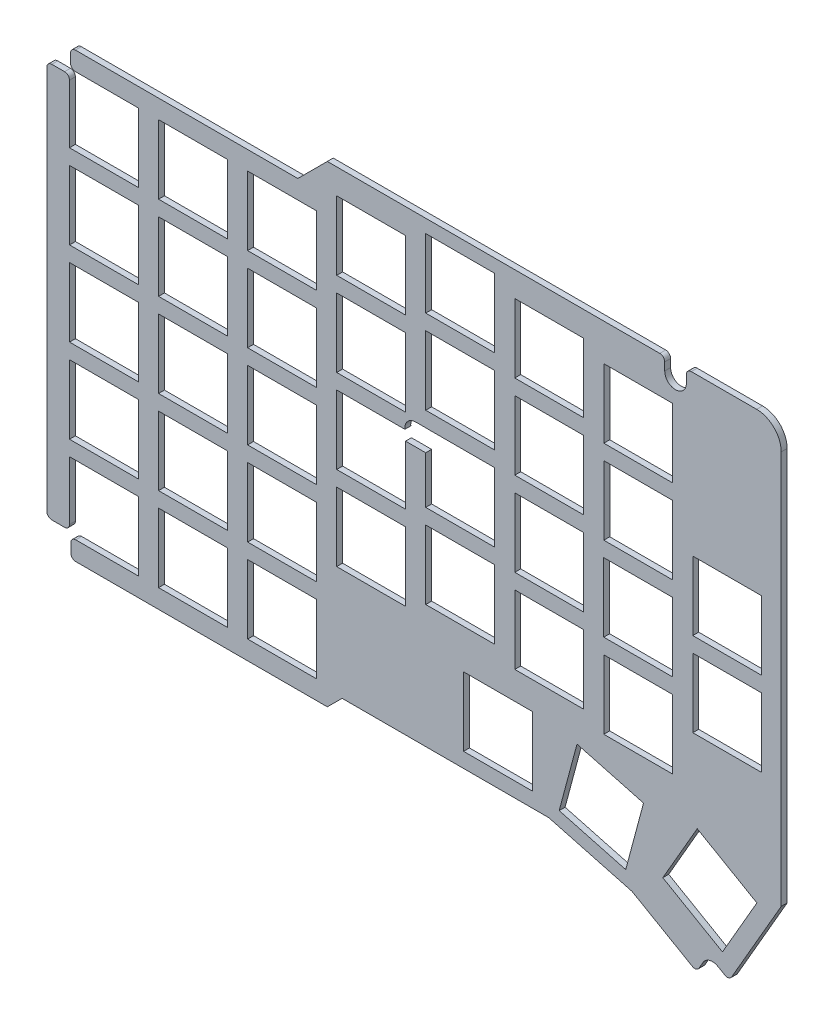
SolidWorks part; units mm, degrees
ref_plane "Front Plane" through (0, 0, 0) normal (0, 0, 1) x (1, 0, 0)
ref_plane "Top Plane" through (0, 0, 0) normal (0, 1, 0) x (1, 0, 0)
ref_plane "Right Plane" through (0, 0, 0) normal (1, 0, 0) x (0, 0, -1)
sketch "Sketch1" plane through (0, 0, 0) normal (0, 0, 1) x (1, 0, 0)
  line L4 (79.33, -202.9) -> (81.33, -202.9)
  line L5 (79.33, -202.9) -> (76.73, -202.9)
  line L6 (81.53, -200.7) -> (81.53, -201.794)
  line L7 (81.53, -200.7) -> (81.53, -198)
  line L8 (81.6, -285.3) -> (81.6, -284.169)
  line L9 (81.6, -284.169) -> (81.6, -288)
  line L11 (82.73, -198) -> (99.78, -198)
  line L12 (82.73, -198) -> (81.53, -198)
  line L13 (76.73, -212.03) -> (76.73, -202.9)
  line L14 (76.73, -283.1) -> (76.73, -212.03)
  line L15 (104.85, -288) -> (81.6, -288)
  line L16 (133.73, -288) -> (113.94, -288)
  line L17 (136.73, -285) -> (133.73, -288)
  line L18 (152.86, -285) -> (136.73, -285)
  line L19 (178.73, -285) -> (161.94, -285)
  line L20 (195.6595, -289.5167) -> (178.73, -285)
  line L22 (79.4, -283.1) -> (81.33, -283.1)
  line L23 (79.4, -283.1) -> (76.73, -283.1)
  line L24 (202.3, -194.6) -> (202.3, -192)
  line L25 (206.7, -194.6) -> (206.7, -192)
  line L26 (206.7, -192) -> (220.98, -192)
  line L29 (-655.8483, 205.3427) -> (210.0949, -294.7997) construction
  line L31 (225.98, -277) -> (215.3978, -295.3219)
  line L32 (225.98, -256.415) -> (225.98, -277)
  line L33 (225.98, -214.605) -> (225.98, -247.025)
  line L34 (225.98, -197) -> (225.98, -205.215)
  line L35 (179.02, -192) -> (202.3, -192)
  line L36 (136.73, -192) -> (169.96, -192)
  line L37 (133.73, -192) -> (136.73, -192)
  line L38 (127.73, -198) -> (133.73, -192)
  line L39 (108.89, -198) -> (127.73, -198)
  line L40 (152.86, -285) -> (161.94, -285)
  line L41 (225.98, -256.415) -> (225.98, -247.025)
  line L42 (225.98, -205.215) -> (225.98, -214.605)
  line L43 (179.02, -192) -> (169.96, -192)
  line L44 (108.89, -198) -> (99.78, -198)
  line L45 (104.85, -288) -> (113.94, -288)
  line L56 (81.6, -284.169) -> (95.33, -284.169)
  line L57 (81.33, -283.1) -> (81.33, -270.169)
  line L58 (81.33, -270.169) -> (95.33, -270.169)
  line L59 (95.33, -284.169) -> (95.33, -270.169)
  line L62 (99.43, -284.169) -> (113.43, -284.169)
  line L63 (99.43, -284.169) -> (99.43, -270.169)
  line L64 (99.43, -270.169) -> (113.43, -270.169)
  line L65 (113.43, -284.169) -> (113.43, -270.169)
  line L66 (99.43, -284.169) -> (113.43, -270.169) construction
  line L67 (99.43, -270.169) -> (113.43, -284.169) construction
  line L68 (81.33, -267.094) -> (95.33, -267.094)
  line L69 (81.33, -267.094) -> (81.33, -253.094)
  line L70 (81.33, -253.094) -> (95.33, -253.094)
  line L71 (95.33, -267.094) -> (95.33, -253.094)
  line L72 (81.33, -267.094) -> (95.33, -253.094) construction
  line L73 (81.33, -253.094) -> (95.33, -267.094) construction
  line L74 (99.43, -267.094) -> (113.43, -267.094)
  line L75 (99.43, -267.094) -> (99.43, -253.094)
  line L76 (99.43, -253.094) -> (113.43, -253.094)
  line L77 (113.43, -267.094) -> (113.43, -253.094)
  line L78 (99.43, -267.094) -> (113.43, -253.094) construction
  line L79 (99.43, -253.094) -> (113.43, -267.094) construction
  line L80 (117.53, -267.094) -> (131.53, -267.094)
  line L81 (117.53, -267.094) -> (117.53, -253.094)
  line L82 (117.53, -253.094) -> (131.53, -253.094)
  line L83 (131.53, -267.094) -> (131.53, -253.094)
  line L84 (117.53, -267.094) -> (131.53, -253.094) construction
  line L85 (117.53, -253.094) -> (131.53, -267.094) construction
  line L86 (117.53, -284.169) -> (131.53, -284.169)
  line L87 (117.53, -284.169) -> (117.53, -270.169)
  line L88 (117.53, -270.169) -> (131.53, -270.169)
  line L89 (131.53, -284.169) -> (131.53, -270.169)
  line L90 (117.53, -284.169) -> (131.53, -270.169) construction
  line L91 (117.53, -270.169) -> (131.53, -284.169) construction
  line L96 (192.7472, -271.9113) -> (189.4631, -271.0313)
  line L97 (213.1003, -293.9949) -> (215.3978, -295.3219)
  line L98 (214.036, -290.9811) -> (221.036, -278.8567)
  line L99 (214.036, -290.9811) -> (201.9117, -283.9811)
  line L100 (201.9117, -283.9811) -> (208.9117, -271.8567)
  line L101 (221.036, -278.8567) -> (208.9117, -271.8567)
  line L102 (214.036, -290.9811) -> (208.9117, -271.8567) construction
  line L103 (201.9117, -283.9811) -> (221.036, -278.8567) construction
  line L104 (161.4166, -281.9876) -> (175.4166, -281.9876)
  line L105 (161.4166, -281.9876) -> (161.4166, -267.9876)
  line L106 (161.4166, -267.9876) -> (175.4166, -267.9876)
  line L107 (175.4166, -281.9876) -> (175.4166, -267.9876)
  line L108 (161.4166, -281.9876) -> (175.4166, -267.9876) construction
  line L109 (161.4166, -267.9876) -> (175.4166, -281.9876) construction
  line L110 (171.83, -262.3626) -> (185.83, -262.3626)
  line L111 (171.83, -262.3626) -> (171.83, -248.3626)
  line L112 (171.83, -248.3626) -> (185.83, -248.3626)
  line L113 (185.83, -262.3626) -> (185.83, -248.3626)
  line L114 (171.83, -262.3626) -> (185.83, -248.3626) construction
  line L115 (171.83, -248.3626) -> (185.83, -262.3626) construction
  line L116 (189.9166, -264.7376) -> (203.9166, -264.7376)
  line L117 (189.9166, -264.7376) -> (189.9166, -250.7376)
  line L118 (189.9166, -250.7376) -> (203.9166, -250.7376)
  line L119 (203.9166, -264.7376) -> (203.9166, -250.7376)
  line L120 (189.9166, -264.7376) -> (203.9166, -250.7376) construction
  line L121 (189.9166, -250.7376) -> (203.9166, -264.7376) construction
  line L122 (208.005, -255.4126) -> (222.005, -255.4126)
  line L123 (208.005, -255.4126) -> (208.005, -241.4126)
  line L124 (208.005, -241.4126) -> (222.005, -241.4126)
  line L125 (222.005, -255.4126) -> (222.005, -241.4126)
  line L126 (208.005, -255.4126) -> (222.005, -241.4126) construction
  line L127 (208.005, -241.4126) -> (222.005, -255.4126) construction
  line L128 (208.005, -238.319) -> (222.005, -238.319)
  line L129 (208.005, -238.319) -> (208.005, -224.319)
  line L130 (208.005, -224.319) -> (222.005, -224.319)
  line L131 (222.005, -238.319) -> (222.005, -224.319)
  line L132 (208.005, -238.319) -> (222.005, -224.319) construction
  line L133 (208.005, -224.319) -> (222.005, -238.319) construction
  line L134 (189.905, -247.644) -> (203.905, -247.644)
  line L135 (189.905, -247.644) -> (189.905, -233.644)
  line L136 (189.905, -233.644) -> (203.905, -233.644)
  line L137 (203.905, -247.644) -> (203.905, -233.644)
  line L138 (189.905, -247.644) -> (203.905, -233.644) construction
  line L139 (189.905, -233.644) -> (203.905, -247.644) construction
  line L140 (189.93, -230.569) -> (203.93, -230.569)
  line L141 (189.93, -230.569) -> (189.93, -216.569)
  line L142 (189.93, -216.569) -> (203.93, -216.569)
  line L143 (203.93, -230.569) -> (203.93, -216.569)
  line L144 (189.93, -230.569) -> (203.93, -216.569) construction
  line L145 (189.93, -216.569) -> (203.93, -230.569) construction
  line L146 (189.93, -213.494) -> (203.93, -213.494)
  line L147 (189.93, -213.494) -> (189.93, -199.494)
  line L148 (189.93, -199.494) -> (203.93, -199.494)
  line L149 (203.93, -213.494) -> (203.93, -199.494)
  line L150 (189.93, -213.494) -> (203.93, -199.494) construction
  line L151 (189.93, -199.494) -> (203.93, -213.494) construction
  line L152 (171.83, -211.069) -> (185.83, -211.069)
  line L153 (171.83, -211.069) -> (171.83, -197.069)
  line L154 (171.83, -197.069) -> (185.83, -197.069)
  line L155 (185.83, -211.069) -> (185.83, -197.069)
  line L156 (171.83, -211.069) -> (185.83, -197.069) construction
  line L157 (171.83, -197.069) -> (185.83, -211.069) construction
  line L158 (171.83, -228.169) -> (185.83, -228.169)
  line L159 (171.83, -228.169) -> (171.83, -214.169)
  line L160 (171.83, -214.169) -> (185.83, -214.169)
  line L161 (185.83, -228.169) -> (185.83, -214.169)
  line L162 (171.83, -228.169) -> (185.83, -214.169) construction
  line L163 (171.83, -214.169) -> (185.83, -228.169) construction
  line L164 (171.83, -245.269) -> (185.83, -245.269)
  line L165 (171.83, -245.269) -> (171.83, -231.269)
  line L166 (171.83, -231.269) -> (185.83, -231.269)
  line L167 (185.83, -245.269) -> (185.83, -231.269)
  line L168 (171.83, -245.269) -> (185.83, -231.269) construction
  line L169 (171.83, -231.269) -> (185.83, -245.269) construction
  line L170 (153.73, -242.894) -> (167.73, -242.894)
  line L171 (153.73, -242.894) -> (153.73, -228.894)
  line L172 (153.73, -228.894) -> (167.73, -228.894)
  line L173 (167.73, -242.894) -> (167.73, -228.894)
  line L174 (153.73, -242.894) -> (167.73, -228.894) construction
  line L175 (153.73, -228.894) -> (167.73, -242.894) construction
  line L176 (153.73, -259.9876) -> (167.73, -259.9876)
  line L177 (153.73, -259.9876) -> (153.73, -245.9876)
  line L178 (153.73, -245.9876) -> (167.73, -245.9876)
  line L179 (167.73, -259.9876) -> (167.73, -245.9876)
  line L180 (153.73, -259.9876) -> (167.73, -245.9876) construction
  line L181 (153.73, -245.9876) -> (167.73, -259.9876) construction
  line L182 (135.63, -262.3626) -> (149.63, -262.3626)
  line L183 (135.63, -262.3626) -> (135.63, -248.3626)
  line L184 (135.63, -248.3626) -> (149.63, -248.3626)
  line L185 (149.63, -262.3626) -> (149.63, -248.3626)
  line L186 (135.63, -262.3626) -> (149.63, -248.3626) construction
  line L187 (135.63, -248.3626) -> (149.63, -262.3626) construction
  line L188 (135.63, -245.269) -> (149.63, -245.269)
  line L189 (135.63, -245.269) -> (135.63, -231.269)
  line L190 (135.63, -231.269) -> (149.63, -231.269)
  line L191 (149.63, -245.269) -> (149.63, -231.269)
  line L192 (135.63, -245.269) -> (149.63, -231.269) construction
  line L193 (135.63, -231.269) -> (149.63, -245.269) construction
  line L194 (135.63, -228.194) -> (149.63, -228.194)
  line L195 (135.63, -228.194) -> (135.63, -214.194)
  line L196 (135.63, -214.194) -> (149.63, -214.194)
  line L197 (149.63, -228.194) -> (149.63, -214.194)
  line L198 (135.63, -228.194) -> (149.63, -214.194) construction
  line L199 (135.63, -214.194) -> (149.63, -228.194) construction
  line L200 (153.73, -225.794) -> (167.73, -225.794)
  line L201 (153.73, -225.794) -> (153.73, -211.794)
  line L202 (153.73, -211.794) -> (167.73, -211.794)
  line L203 (167.73, -225.794) -> (167.73, -211.794)
  line L204 (153.73, -225.794) -> (167.73, -211.794) construction
  line L205 (153.73, -211.794) -> (167.73, -225.794) construction
  line L206 (153.73, -208.694) -> (167.73, -208.694)
  line L207 (153.73, -208.694) -> (153.73, -194.694)
  line L208 (153.73, -194.694) -> (167.73, -194.694)
  line L209 (167.73, -208.694) -> (167.73, -194.694)
  line L210 (153.73, -208.694) -> (167.73, -194.694) construction
  line L211 (153.73, -194.694) -> (167.73, -208.694) construction
  line L212 (135.63, -211.094) -> (149.63, -211.094)
  line L213 (135.63, -211.094) -> (135.63, -197.094)
  line L214 (135.63, -197.094) -> (149.63, -197.094)
  line L215 (149.63, -211.094) -> (149.63, -197.094)
  line L216 (135.63, -211.094) -> (149.63, -197.094) construction
  line L217 (135.63, -197.094) -> (149.63, -211.094) construction
  line L218 (117.53, -215.794) -> (131.53, -215.794)
  line L219 (117.53, -215.794) -> (117.53, -201.794)
  line L220 (117.53, -201.794) -> (131.53, -201.794)
  line L221 (131.53, -215.794) -> (131.53, -201.794)
  line L222 (117.53, -215.794) -> (131.53, -201.794) construction
  line L223 (117.53, -201.794) -> (131.53, -215.794) construction
  line L224 (117.53, -232.894) -> (131.53, -232.894)
  line L225 (117.53, -232.894) -> (117.53, -218.894)
  line L226 (117.53, -218.894) -> (131.53, -218.894)
  line L227 (131.53, -232.894) -> (131.53, -218.894)
  line L228 (117.53, -232.894) -> (131.53, -218.894) construction
  line L229 (117.53, -218.894) -> (131.53, -232.894) construction
  line L230 (117.53, -249.994) -> (131.53, -249.994)
  line L231 (117.53, -249.994) -> (117.53, -235.994)
  line L232 (117.53, -235.994) -> (131.53, -235.994)
  line L233 (131.53, -249.994) -> (131.53, -235.994)
  line L234 (117.53, -249.994) -> (131.53, -235.994) construction
  line L235 (117.53, -235.994) -> (131.53, -249.994) construction
  line L236 (99.43, -249.994) -> (113.43, -249.994)
  line L237 (99.43, -249.994) -> (99.43, -235.994)
  line L238 (99.43, -235.994) -> (113.43, -235.994)
  line L239 (113.43, -249.994) -> (113.43, -235.994)
  line L240 (99.43, -249.994) -> (113.43, -235.994) construction
  line L241 (99.43, -235.994) -> (113.43, -249.994) construction
  line L242 (81.33, -249.994) -> (95.33, -249.994)
  line L243 (81.33, -249.994) -> (81.33, -235.994)
  line L244 (81.33, -235.994) -> (95.33, -235.994)
  line L245 (95.33, -249.994) -> (95.33, -235.994)
  line L246 (81.33, -249.994) -> (95.33, -235.994) construction
  line L247 (81.33, -235.994) -> (95.33, -249.994) construction
  line L248 (81.33, -232.894) -> (95.33, -232.894)
  line L249 (81.33, -232.894) -> (81.33, -218.894)
  line L250 (81.33, -218.894) -> (95.33, -218.894)
  line L251 (95.33, -232.894) -> (95.33, -218.894)
  line L252 (81.33, -232.894) -> (95.33, -218.894) construction
  line L253 (81.33, -218.894) -> (95.33, -232.894) construction
  line L254 (99.43, -232.894) -> (113.43, -232.894)
  line L255 (99.43, -232.894) -> (99.43, -218.894)
  line L256 (99.43, -218.894) -> (113.43, -218.894)
  line L257 (113.43, -232.894) -> (113.43, -218.894)
  line L258 (99.43, -232.894) -> (113.43, -218.894) construction
  line L259 (99.43, -218.894) -> (113.43, -232.894) construction
  line L260 (99.43, -215.794) -> (113.43, -215.794)
  line L261 (99.43, -215.794) -> (99.43, -201.794)
  line L262 (99.43, -201.794) -> (113.43, -201.794)
  line L263 (113.43, -215.794) -> (113.43, -201.794)
  line L264 (99.43, -215.794) -> (113.43, -201.794) construction
  line L265 (99.43, -201.794) -> (113.43, -215.794) construction
  line L266 (81.33, -215.794) -> (95.33, -215.794)
  line L267 (81.33, -215.794) -> (81.33, -202.9)
  line L268 (81.53, -201.794) -> (95.33, -201.794)
  line L269 (95.33, -215.794) -> (95.33, -201.794)
  line L270 (210.0949, -294.7997) -> (208.7784, -297.081)
  line L271 (208.7784, -297.081) -> (195.6595, -289.5167)
  line L272 (180.8526, -282.6996) -> (194.3756, -286.3231)
  line L273 (180.8526, -282.6996) -> (184.4761, -269.1766)
  line L274 (184.4761, -269.1766) -> (197.999, -272.8001)
  line L275 (194.3756, -286.3231) -> (197.999, -272.8001)
  line L276 (180.8526, -282.6996) -> (197.999, -272.8001) construction
  line L277 (184.4761, -269.1766) -> (194.3756, -286.3231) construction
  line L279 (213.1003, -293.9949) -> (25219.1187, 43001.2594) construction
  arc A1 (225.98, -197) -> (220.98, -192) centre (220.98, -197) ccw
  arc A8 (211.4498, -296.8525) -> (211.4505, -296.8529) centre (212, -295.9) ccw
  arc A10 (210.8997, -297.8051) -> (210.9011, -297.8059) centre (212, -295.9) ccw
  circle A46 centre (88.33, -260.094) radius 1.725
  circle A47 centre (106.43, -260.094) radius 1.725
  circle A48 centre (106.43, -277.169) radius 1.725
  circle A49 centre (124.53, -277.169) radius 1.725
  circle A50 centre (124.53, -260.094) radius 1.725
  circle A51 centre (142.63, -255.3626) radius 1.725
  circle A52 centre (160.73, -252.9876) radius 1.725
  circle A53 centre (178.83, -255.3626) radius 1.725
  circle A54 centre (168.4166, -274.9876) radius 1.725
  circle A55 centre (189.4258, -277.7499) radius 1.725
  circle A56 centre (211.4738, -281.4189) radius 1.725
  circle A57 centre (196.9166, -257.7376) radius 1.725
  circle A58 centre (215.005, -248.4126) radius 1.725
  circle A59 centre (215.005, -231.319) radius 1.725
  circle A60 centre (196.905, -240.644) radius 1.725
  circle A61 centre (178.83, -238.269) radius 1.725
  circle A62 centre (160.73, -235.894) radius 1.725
  circle A63 centre (142.63, -238.269) radius 1.725
  circle A64 centre (124.53, -242.994) radius 1.725
  circle A65 centre (106.43, -242.994) radius 1.725
  circle A66 centre (88.33, -242.994) radius 1.725
  circle A67 centre (88.33, -225.894) radius 1.725
  circle A68 centre (106.43, -225.894) radius 1.725
  circle A69 centre (124.53, -225.894) radius 1.725
  circle A70 centre (142.63, -221.194) radius 1.725
  circle A71 centre (160.73, -218.794) radius 1.725
  circle A72 centre (178.83, -221.169) radius 1.725
  circle A73 centre (196.93, -223.569) radius 1.725
  circle A74 centre (196.93, -206.494) radius 1.725
  circle A75 centre (178.83, -204.069) radius 1.725
  circle A76 centre (160.73, -201.694) radius 1.725
  circle A77 centre (142.63, -204.094) radius 1.725
  circle A78 centre (124.53, -208.794) radius 1.725
  circle A79 centre (106.43, -208.794) radius 1.725
  arc A85 (202.3, -194.6) -> (206.7, -194.6) centre (204.5, -194.6) ccw
  arc A88 (213.1003, -293.9949) -> (210.0941, -294.8011) centre (212, -295.9) ccw
  dimension "D73" = 4.4
  dimension "D74" = 4.4
  dimension "D2" = 14
  dimension "D3" = 14
  dimension "D4" = 14
  dimension "D5" = 14
  dimension "D6" = 14
  dimension "D7" = 14
  dimension "D8" = 14
  dimension "D9" = 14
  dimension "D10" = 14
  dimension "D11" = 14
  dimension "D12" = 14
  dimension "D13" = 14
  dimension "D14" = 14
  dimension "D15" = 14
  dimension "D16" = 14
  dimension "D17" = 14
  dimension "D18" = 14
  dimension "D19" = 14
  dimension "D20" = 14
  dimension "D21" = 14
  dimension "D22" = 14
  dimension "D23" = 14
  dimension "D24" = 14
  dimension "D25" = 14
  dimension "D26" = 14
  dimension "D27" = 14
  dimension "D28" = 14
  dimension "D29" = 14
  dimension "D30" = 14
  dimension "D31" = 14
  dimension "D32" = 14
  dimension "D33" = 14
  dimension "D34" = 14
  dimension "D35" = 14
  dimension "D36" = 14
  dimension "D37" = 14
  dimension "D38" = 14
  dimension "D39" = 14
  dimension "D40" = 14
  dimension "D41" = 14
  dimension "D42" = 14
  dimension "D43" = 14
  dimension "D44" = 14
  dimension "D45" = 14
  dimension "D46" = 14
  dimension "D47" = 14
  dimension "D48" = 14
  dimension "D49" = 14
  dimension "D50" = 14
  dimension "D51" = 14
  dimension "D52" = 14
  dimension "D53" = 14
  dimension "D54" = 14
  dimension "D55" = 14
  dimension "D56" = 14
  dimension "D57" = 14
  dimension "D58" = 14
  dimension "D59" = 14
  dimension "D60" = 14
  dimension "D61" = 14
  dimension "D62" = 14
  dimension "D63" = 14
  dimension "D64" = 14
  dimension "D65" = 14
  dimension "D66" = 14
  dimension "D67" = 14
  dimension "D68" = 14
  dimension "D69" = 14
  dimension "D70" = 14
  dimension "D71" = 14
  dimension "D72" = 14
extrude "Boss-Extrude2" add sketch "Sketch1" along normal blind 1.2 contours A88 L97 L31 L32 L41 L33 L42 L34 A1 L26 L25 A85 L24 L35 L43 L36 L37 L38 L39 L44 L11 L12 L7 L6 L268 L269 L266 L267 L4 L5 L13 L14 L23 L22 L57 L58 L59 L56 L8 L9 L15 L45 L16 L17 L18 L40 L19 L20 L271 L270
fillet "Fillet1" radius 1 12 edges at (215.3978, -295.3219, 0.6) (208.7784, -297.081, 0.6) (206.7, -192, 0.6) (202.3, -192, 0.6) (81.53, -198, 0.6) (76.73, -202.9, 0.6) (81.33, -202.9, 0.6) (81.53, -201.794, 0.6) (76.73, -283.1, 0.6) (81.6, -288, 0.6) (81.33, -283.1, 0.6) (81.6, -284.169, 0.6)
sketch "Sketch2" plane through (0, 0, 1.2) normal (0, 0, 1) x (1, 0, 0)
  line L0 (133.73, -192) -> (201.3, -192) construction
  line L1 (76.73, -282.1) -> (76.73, -203.9) construction
  line L2 (151.68, -228.88) -> (153.73, -228.88)
  line L3 (153.73, -242.894) -> (153.73, -228.894) construction
  line L4 (153.73, -228.88) -> (153.73, -228.894)
  line L5 (151.68, -233.28) -> (149.63, -233.28)
  line L6 (149.63, -245.269) -> (149.63, -231.269) construction
  line L7 (149.63, -233.28) -> (149.63, -231.8784)
  line L8 (151.68, -233.28) -> (153.73, -233.28)
  line L9 (153.73, -233.28) -> (153.73, -231.8784)
  line L10 (153.73, -228.894) -> (153.73, -230.2816)
  circle A0 centre (151.68, -231.08) radius 1.1 construction
  circle A1 centre (151.68, -231.08) radius 2.2
  dimension "D1" = 2.2
  dimension "D4" = 4.4
  dimension "D2" = 39.08
  dimension "D3" = 74.95
extrude "Cut-Extrude2" cut sketch "Sketch2" against normal up to next contours A1 L10 L4 L2 | A1 | A1 L8 L9 | A1 L7 L5
